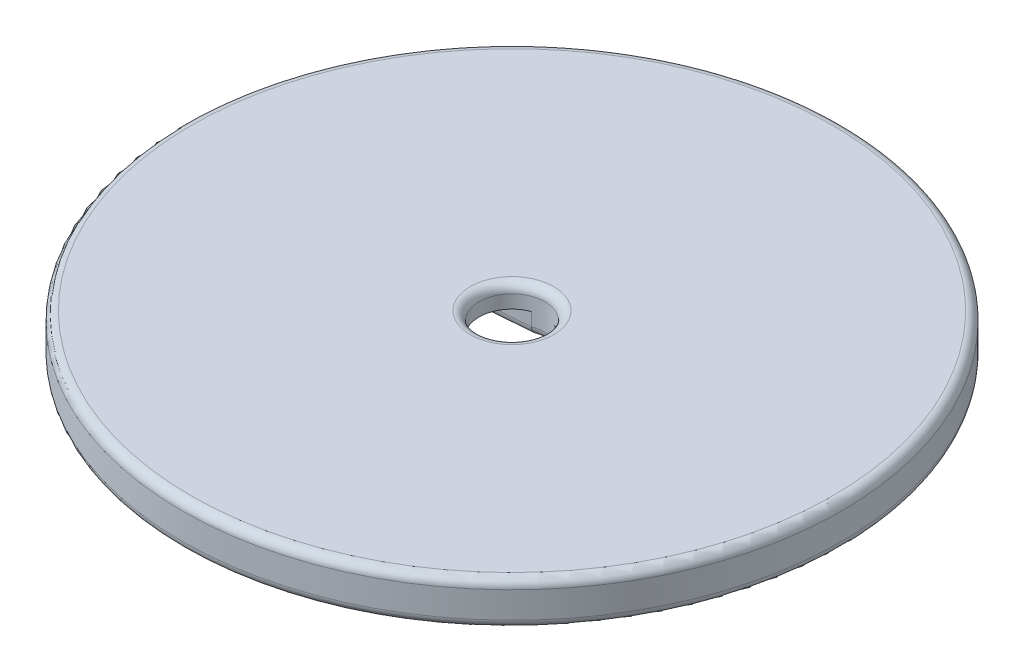
SolidWorks part; units mm, degrees
ref_plane "Front Plane" through (0, 0, 0) normal (0, 0, 1) x (1, 0, 0)
ref_plane "Top Plane" through (0, 0, 0) normal (0, 1, 0) x (1, 0, 0)
ref_plane "Right Plane" through (0, 0, 0) normal (1, 0, 0) x (0, 0, -1)
sketch "Sketch1" plane through (0, 0, 0) normal (0, 1, 0) x (1, 0, 0)
  circle A0 centre (0, 0) radius 37.5
  circle A1 centre (0, 0) radius 3.75
  point P0 (0, 0)
  dimension "D1" = 75
  dimension "D2" = 7.5
extrude "Boss-Extrude1" add sketch "Sketch1" along normal blind 5
sketch "Sketch2" plane through (0, 0, 0) normal (0, -1, 0) x (1, 0, 0)
  line L0 (-36.7746, 0) -> (-11.5, 0) construction
  line L1 (-14, 2.5) -> (-1.2261, 3.5439)
  line L2 (14, 2.5) -> (1.2261, 3.5439)
  line L3 (-1.3079, -3.5145) -> (-1.3079, -10.0551) construction
  line L4 (-1.3079, -3.5145) -> (-14, -2.5)
  line L5 (1.3079, -3.5145) -> (1.3079, -9.6833) construction
  line L6 (14, -2.5) -> (1.3079, -3.5145)
  line L7 (-4, 0) -> (36.7746, 0) construction
  arc A0 (14, -2.5) -> (14, 2.5) centre (14, 0) ccw
  arc A1 (-14, 2.5) -> (-14, -2.5) centre (-14, 0) ccw
  circle A2 centre (0, 0) radius 3.75 construction
  arc A3 (1.2261, 3.5439) -> (-1.2261, 3.5439) centre (0, 0) ccw
  arc A4 (-1.3079, -3.5145) -> (1.3079, -3.5145) centre (0, 0) ccw
  point P5 (0, 0)
  dimension "D1" = 5
  dimension "D2" = 14
  dimension "D3" = 14
extrude "Cut-Extrude1" cut sketch "Sketch2" against normal blind 2.5
fillet "Fillet1" radius 1 11 edges at (0, 5, 3.75) (0, 5, 37.5) (-7.6131, 0, 3.0219) (-16.5, 0, 0) (-7.6539, 0, -3.0073) (0, 0, -3.75) (7.6539, 0, -3.0073) (16.5, 0, 0) (7.6131, 0, 3.0219) (0, 0, 3.75) (0, 0, 37.5)
